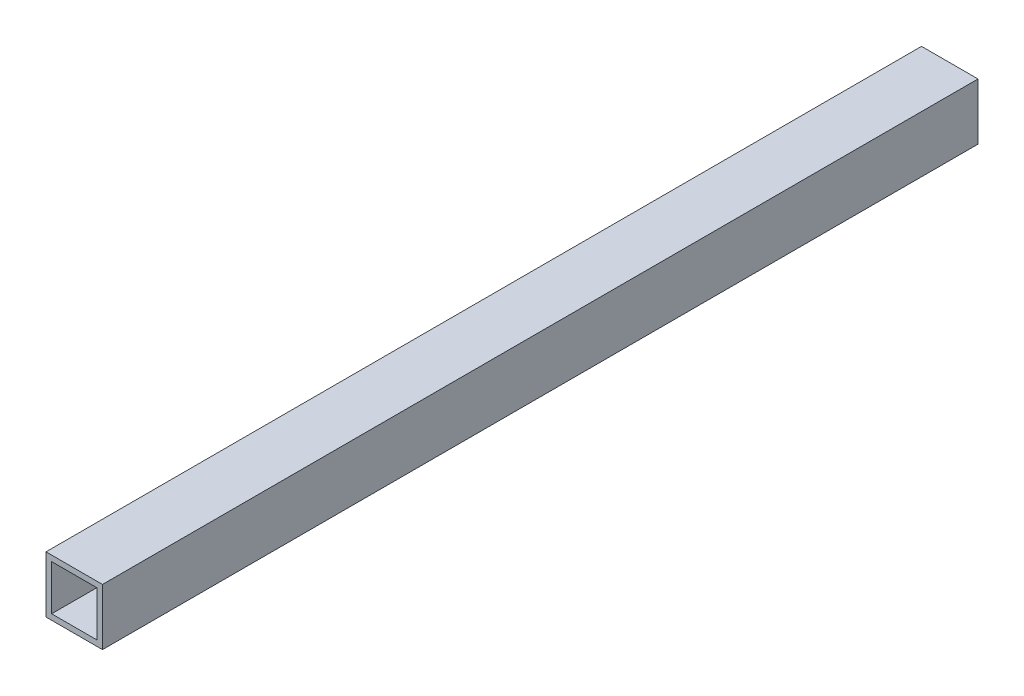
SolidWorks part; units mm, degrees
material "1.0037 (S235JR)"
ref_plane "Front Plane" through (0, 0, 0) normal (0, 0, 1) x (1, 0, 0)
ref_plane "Top Plane" through (0, 0, 0) normal (0, 1, 0) x (1, 0, 0)
ref_plane "Right Plane" through (0, 0, 0) normal (1, 0, 0) x (0, 0, -1)
curve "Curve1"
  spline degree 1 poles (0, 0, 0) (0, 0, 620) knots 0 0 1 1
sketch "Sketch1" plane through (0, 0, 0) normal (0, 0, 1) x (1, 0, 0)
  line L0 (0, 35.3535) -> (0, -33.8384) construction
  line L1 (-20, 20) -> (20, 20)
  line L2 (-20, 20) -> (-20, -20)
  line L3 (-20, -20) -> (20, -20)
  line L4 (20, 20) -> (20, -20)
  line L5 (-16, 16) -> (16, 16)
  line L6 (-16, 16) -> (-16, -16)
  line L7 (-16, -16) -> (16, -16)
  line L8 (16, 16) -> (16, -16)
  line L9 (-39.3939, 0) -> (41.5152, 0) construction
  dimension "D1" = 40
  dimension "D2" = 32
sweep "Sweep1" add profiles "Sketch1" path "Curve1"
